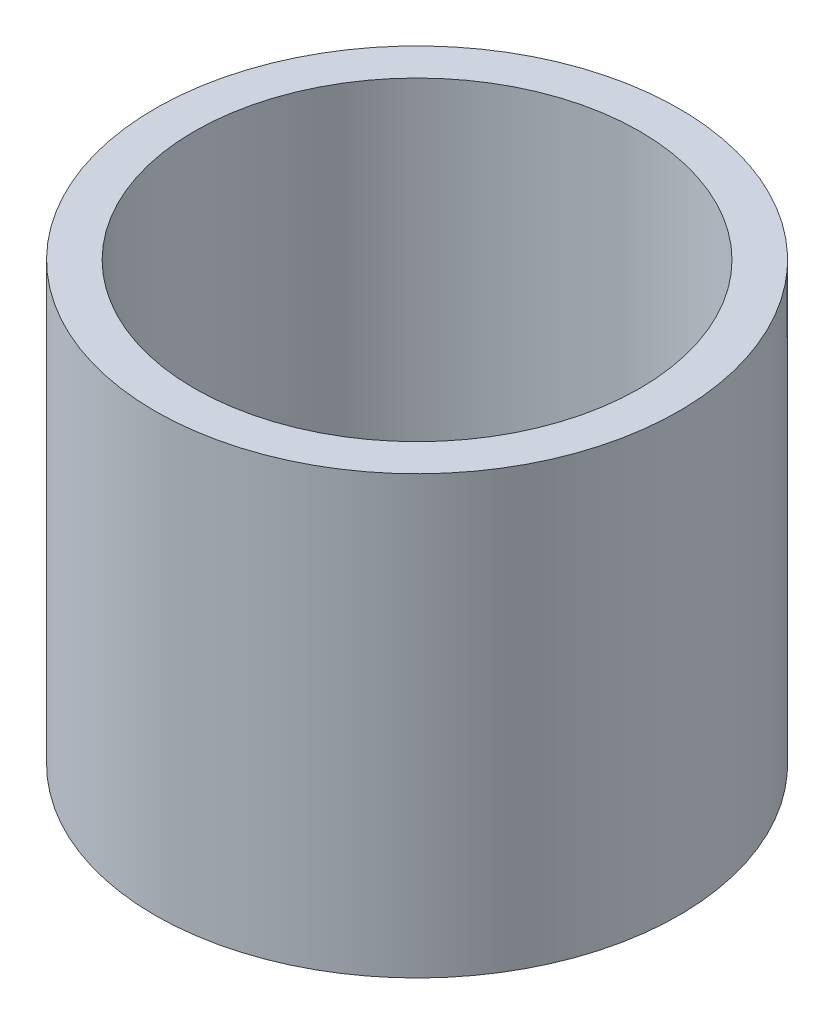
SolidWorks part; units mm, degrees
material "1060 Alloy"
ref_plane "Front Plane" through (0, 0, 0) normal (0, 0, 1) x (1, 0, 0)
ref_plane "Top Plane" through (0, 0, 0) normal (0, 1, 0) x (1, 0, 0)
ref_plane "Right Plane" through (0, 0, 0) normal (1, 0, 0) x (0, 0, -1)
sketch "Sketch1" plane through (0, 0, 0) normal (0, 0, 1) x (1, 0, 0)
  line L0 (0, 0) -> (2.15, 0) construction
  line L1 (2.15, 2.5) -> (3, 2.5)
  line L2 (2.15, 2.5) -> (2.15, -2.5)
  line L3 (2.15, -2.5) -> (3, -2.5)
  line L4 (3, 2.5) -> (3, -2.5)
  line L5 (0, 9.8862) -> (0, -9.8862) construction
  dimension "D1" = 5
  dimension "D2" = 6
  dimension "D3" = 4.3
revolve "Revolve1" add sketch "Sketch1" angle 360 about L5
sketch "Sketch2" plane through (0, 2.5, 0) normal (0, 1, 0) x (1, 0, 0)
  circle A0 centre (0, 0) radius 2.55
  dimension "D1" = 5.1
extrude "Cut-Extrude1" cut sketch "Sketch2" against normal through all
